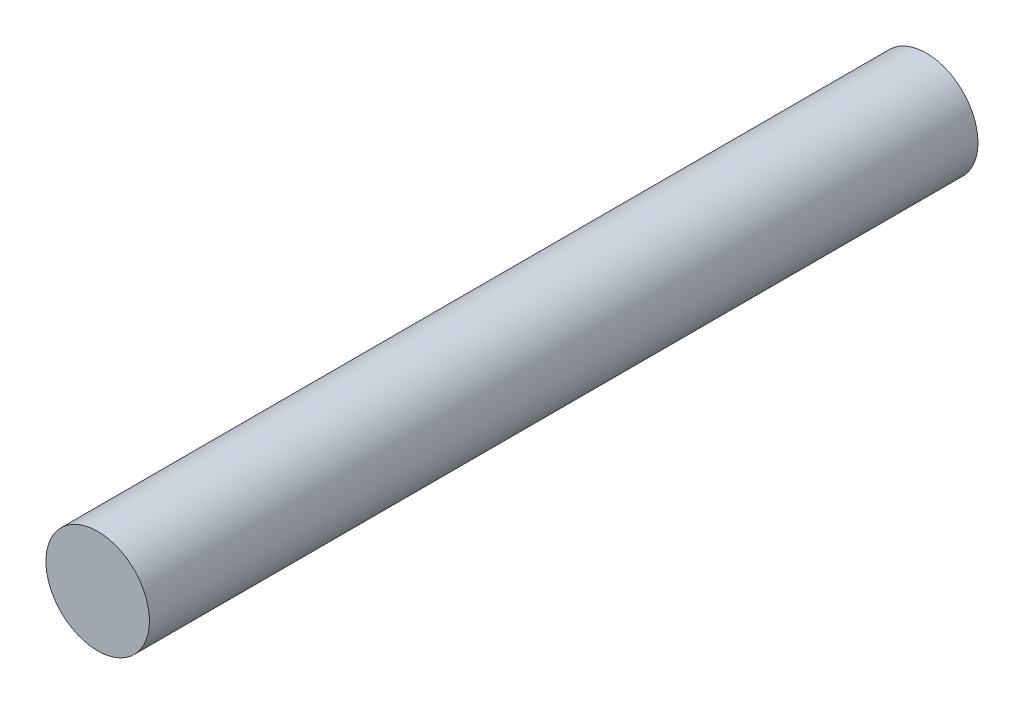
SolidWorks part; units mm, degrees
ref_plane "Front Plane" through (0, 0, 0) normal (0, 0, 1) x (1, 0, 0)
ref_plane "Top Plane" through (0, 0, 0) normal (0, 1, 0) x (1, 0, 0)
ref_plane "Right Plane" through (0, 0, 0) normal (1, 0, 0) x (0, 0, -1)
sketch "Sketch1" plane through (0, 0, 0) normal (0, 0, 1) x (1, 0, 0)
  circle A0 centre (0, 0) radius 1.875
  dimension "D1" = 3.75
extrude "Boss-Extrude1" add sketch "Sketch1" along normal blind 30
